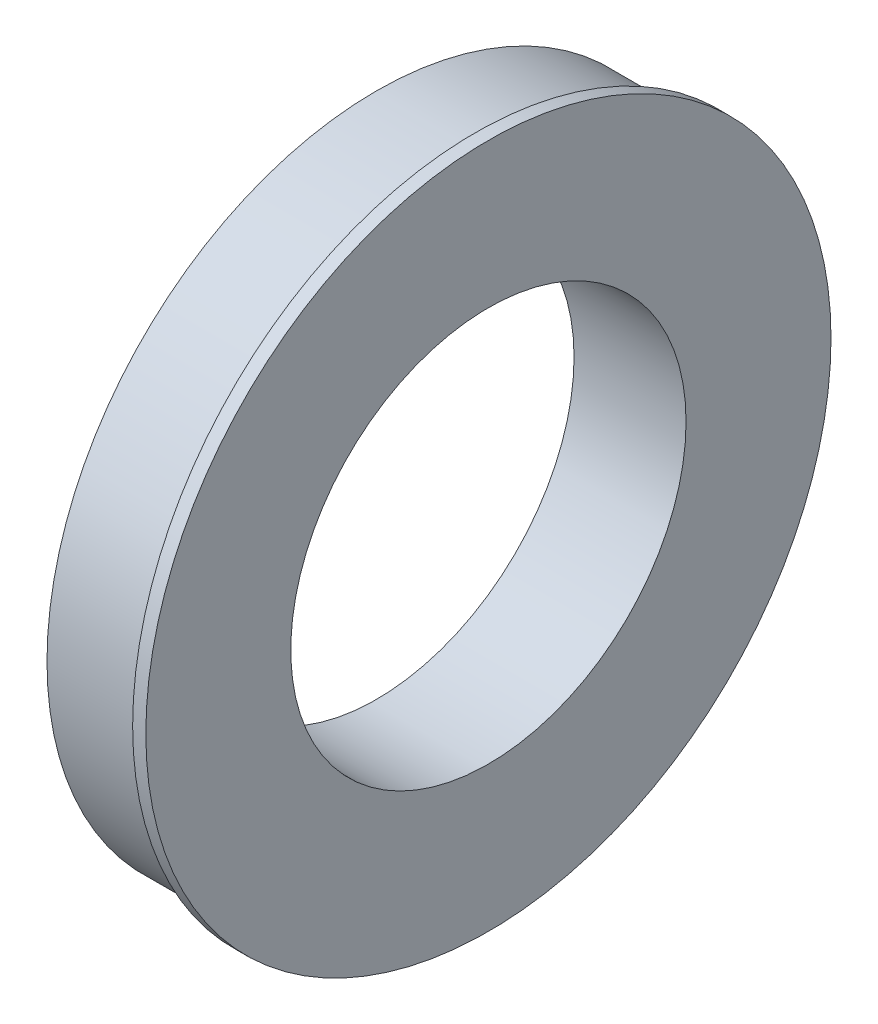
SolidWorks part; units mm, degrees
ref_plane "Plan de face" through (0, 0, 0) normal (0, 0, 1) x (1, 0, 0)
ref_plane "Plan de dessus" through (0, 0, 0) normal (0, 1, 0) x (1, 0, 0)
ref_plane "Plan de droite" through (0, 0, 0) normal (1, 0, 0) x (0, 0, -1)
sketch "Esquisse1" plane through (0, 0, 0) normal (1, 0, 0) x (0, 0, -1)
  circle A0 centre (0, 0) radius 38.1
  circle A1 centre (0, 0) radius 63.5
  dimension "D1" = 127
  dimension "D2" = 76.2
extrude "Boss.-Extru.1" add sketch "Esquisse1" along normal mid plane 19.05
sketch "Esquisse2" plane through (9.525, 0, 0) normal (1, 0, 0) x (0, 0, -1)
  circle A1 centre (0, 0) radius 38.1 construction
  circle A2 centre (0, 0) radius 66.04
  circle A3 centre (0, 0) radius 66.04
  circle A4 centre (0, 0) radius 38.1
  dimension "D1" = 2.54
extrude "Boss.-Extru.2" add sketch "Esquisse2" along normal blind 2.54
